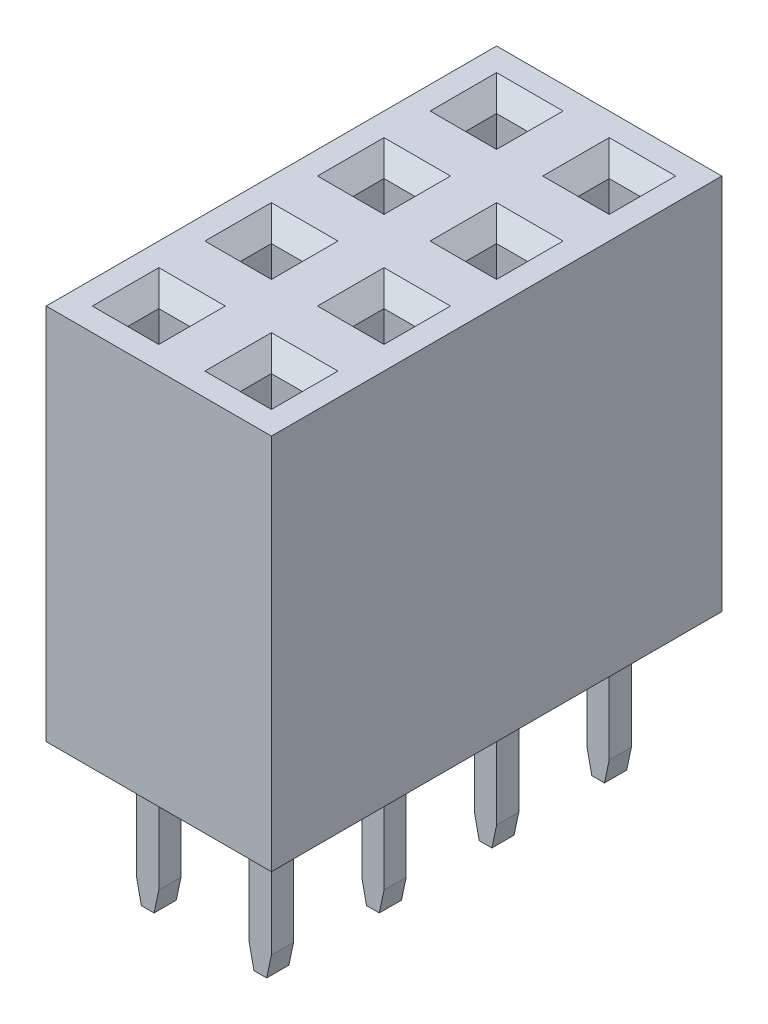
SolidWorks part; units mm, degrees
ref_plane "Спереди" through (0, 0, 0) normal (0, 0, 1) x (1, 0, 0)
ref_plane "Сверху" through (0, 0, 0) normal (0, 1, 0) x (1, 0, 0)
ref_plane "Справа" through (0, 0, 0) normal (1, 0, 0) x (0, 0, -1)
ref_plane "Плоскость1" through (0, 0, 0) normal (0, 1, 0) x (-1, 0, 0)
sketch "Эскиз1" plane through (0, 0, 0) normal (0, 1, 0) x (-1, 0, 0)
  line L0 (0, 0) -> (-5.5295, 0) construction
  line L1 (0, 0) -> (0, -2.1715) construction
  line L2 (-1.27, 1.27) -> (1.27, 1.27)
  line L3 (-1.27, 1.27) -> (-1.27, -1.27)
  line L4 (-1.27, -1.27) -> (1.27, -1.27)
  line L5 (1.27, 1.27) -> (1.27, -1.27)
  point P0 (-1.27, 1.27)
  point P1 (1.27, -1.27)
  point P2 (-1.27, -1.27)
  point P3 (1.27, 1.27)
  dimension "D1" = 2.54
  dimension "D6" = 1.27
extrude "Бобышка-Вытянуть1" add sketch "Эскиз1" along normal blind 8.51
sketch "Эскиз4" plane through (0, 8.51, 0) normal (0, 1, 0) x (1, 0, 0)
  line L0 (0, 0) -> (0.806, 0) construction
  line L1 (0, 0) -> (0, 1.2961) construction
  line L3 (-0.35, 0.35) -> (0.35, 0.35)
  line L4 (-0.35, 0.35) -> (-0.35, -0.35)
  line L5 (-0.35, -0.35) -> (0.35, -0.35)
  line L6 (0.35, 0.35) -> (0.35, -0.35)
  dimension "D1" = 0.7
extrude "Вырез-Вытянуть1" cut sketch "Эскиз4" against normal blind 8.21
chamfer "Фаска3" distance 0.4 angle 45 4 edges at (0.35, 8.51, 0) (0, 8.51, -0.35) (0, 8.51, 0.35) (-0.35, 8.51, 0)
sketch "Эскиз2" plane through (0, 0, 0) normal (0, 1, 0) x (-1, 0, 0)
  line L0 (0, 0) -> (0, -0.4454) construction
  line L1 (0.25, 0.25) -> (-0.25, 0.25)
  line L2 (0.25, 0.25) -> (0.25, -0.25)
  line L3 (0.25, -0.25) -> (-0.25, -0.25)
  line L4 (-0.25, 0.25) -> (-0.25, -0.25)
  line L5 (0, 0) -> (-0.4704, 0) construction
  dimension "D1" = 0.5
  dimension "D2" = 0.5
extrude "Бобышка-Вытянуть2" add sketch "Эскиз2" against normal blind 3.15
chamfer "Фаска2" distance 0.5 angle 12 2 edges at (0.25, -3.15, 0) (-0.25, -3.15, 0)
pattern_linear "Линейный массив1" count 4 spacing 2.54 along (0, 0, -1) count 2 spacing 2.54 along (-1, 0, 0) of "Бобышка-Вытянуть1", "Вырез-Вытянуть1", "Фаска3", "Бобышка-Вытянуть2", "Фаска2"
equation "\"D6@Эскиз1\"=2.54/2"
